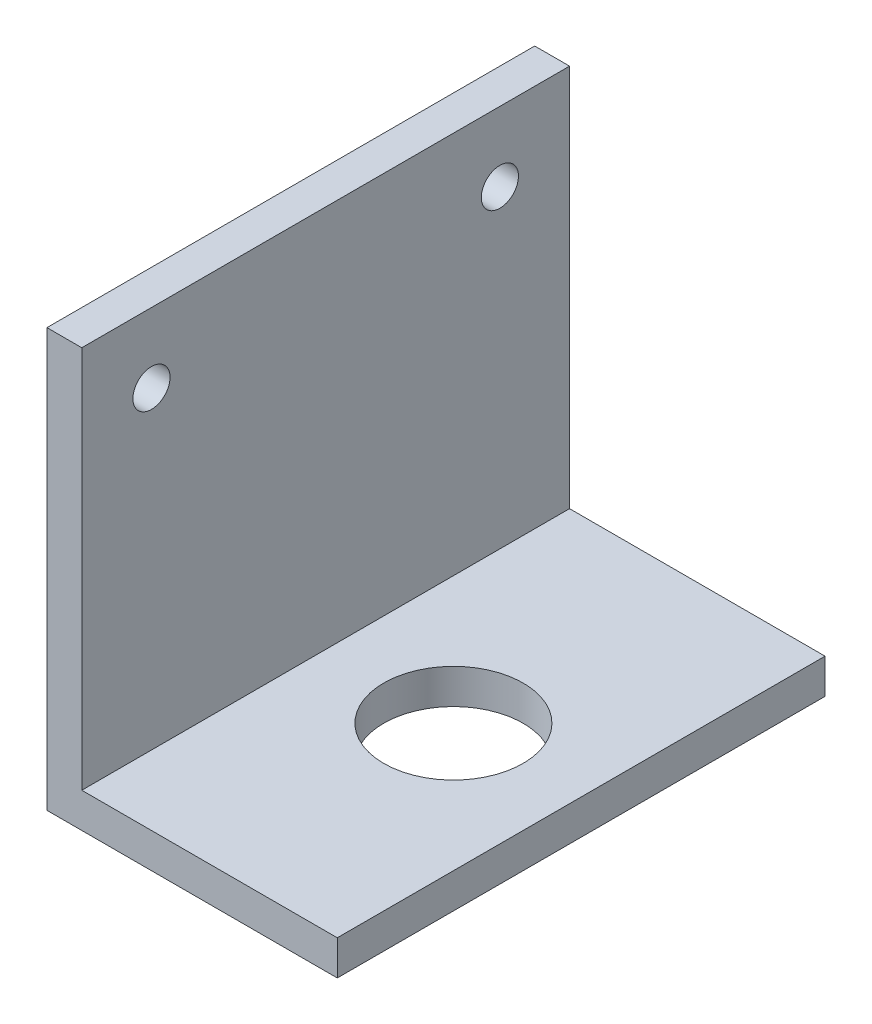
SolidWorks part; units mm, degrees
material "1060 合金"
ref_plane "正面" through (0, 0, 0) normal (0, 0, 1) x (1, 0, 0)
ref_plane "平面" through (0, 0, 0) normal (0, 1, 0) x (1, 0, 0)
ref_plane "右側面" through (0, 0, 0) normal (1, 0, 0) x (0, 0, -1)
sketch "ｽｹｯﾁ1" plane through (0, 0, 0) normal (0, 0, 1) x (1, 0, 0)
  line L0 (0, 0) -> (0, 36)
  line L1 (0, 36) -> (3, 36)
  line L2 (3, 36) -> (3, 3)
  line L3 (3, 3) -> (25, 3)
  line L4 (25, 3) -> (25, 0)
  line L5 (25, 0) -> (0, 0)
  dimension "D1" = 36
  dimension "D2" = 25
  dimension "D3" = 3
  dimension "D4" = 3
extrude "ﾎﾞｽ - 押し出し1" add sketch "ｽｹｯﾁ1" along normal blind 42
sketch "ｽｹｯﾁ2" plane through (0, 0, 0) normal (-1, 0, 0) x (0, 0, 1)
  line L0 (42, 36) -> (42, 0) construction
  line L3 (42, 36) -> (0, 36) construction
  line L4 (0, 36) -> (0, 0) construction
  circle A0 centre (36, 30) radius 1.6
  circle A2 centre (6, 30) radius 1.6
  dimension "D1" = 6
  dimension "D2" = 6
  dimension "D3" = 6
  dimension "D4" = 3.2
extrude "ｶｯﾄ - 押し出し1" cut sketch "ｽｹｯﾁ2" against normal through all
sketch "ｽｹｯﾁ3" plane through (0, 3, 0) normal (0, 1, 0) x (1, 0, 0)
  line L0 (25, -42) -> (25, 0) construction
  line L1 (25, -42) -> (3, -42) construction
  circle A0 centre (14, -21) radius 6
  dimension "D1" = 12
  dimension "D2" = 11
  dimension "D3" = 21
extrude "ｶｯﾄ - 押し出し2" cut sketch "ｽｹｯﾁ3" against normal through all
